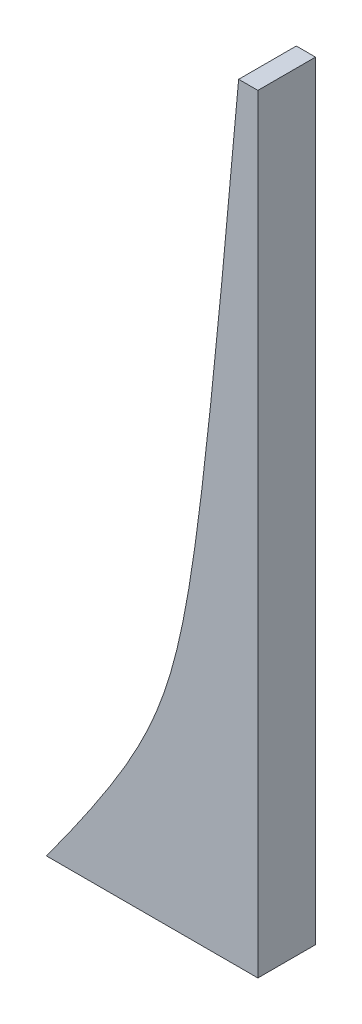
SolidWorks part; units mm, degrees
ref_plane "Front Plane" through (0, 0, 0) normal (0, 0, 1) x (1, 0, 0)
ref_plane "Top Plane" through (0, 0, 0) normal (0, 1, 0) x (1, 0, 0)
ref_plane "Right Plane" through (0, 0, 0) normal (1, 0, 0) x (0, 0, -1)
sketch "Sketch1" plane through (0, 0, 0) normal (0, 0, 1) x (1, 0, 0)
  line L1 (0, 0) -> (11, 0)
  line L3 (10, 40) -> (11, 40)
  line L4 (11, 0) -> (11, 40)
  conic Q0 (10, 40) -> (0, 0) control (7.3399, 10.0964) rho 0.75
  dimension "D2" = 1
  dimension "40" = 40
extrude "Boss-Extrude1" add sketch "Sketch1" along normal blind 3 contours L1 L4 L3 Q0
